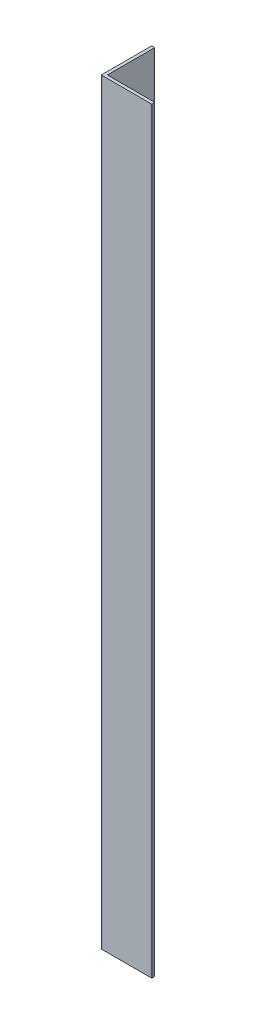
SolidWorks part; units mm, degrees
material "1060 Сплав"
ref_plane "Спереди" through (0, 0, 0) normal (0, 0, 1) x (1, 0, 0)
ref_plane "Сверху" through (0, 0, 0) normal (0, 1, 0) x (1, 0, 0)
ref_plane "Справа" through (0, 0, 0) normal (1, 0, 0) x (0, 0, -1)
sketch "уголок-20х20" plane through (0, 0, 0) normal (0, 1, 0) x (1, 0, 0)
  line L0 (-10.9179, 0.2) -> (-10.9179, 19.8)
  line L1 (-10.7179, 20) -> (-9.9179, 20)
  line L2 (-9.7179, 19.8) -> (-9.7179, 1.4)
  line L3 (-9.5179, 1.2) -> (8.8821, 1.2)
  line L4 (9.0821, 1) -> (9.0821, 0.2)
  line L5 (8.8821, 0) -> (-10.7179, 0)
  arc A0 (9.0821, 0.2) -> (8.8821, 0) centre (8.8821, 0.2) cw
  arc A1 (8.8821, 1.2) -> (9.0821, 1) centre (8.8821, 1) cw
  arc A2 (-9.7179, 1.4) -> (-9.5179, 1.2) centre (-9.5179, 1.4) ccw
  arc A3 (-10.9179, 0.2) -> (-10.7179, 0) centre (-10.7179, 0.2) ccw
  arc A4 (-9.9179, 20) -> (-9.7179, 19.8) centre (-9.9179, 19.8) cw
  arc A5 (-10.9179, 19.8) -> (-10.7179, 20) centre (-10.7179, 19.8) cw
  point P2 (0, 0)
  dimension "D4" = 0.2
  dimension "D1" = 20
  dimension "D2" = 20
  dimension "D3" = 1.2
extrude "Бобышка-Вытянуть1" add sketch "уголок-20х20" along normal blind 300
